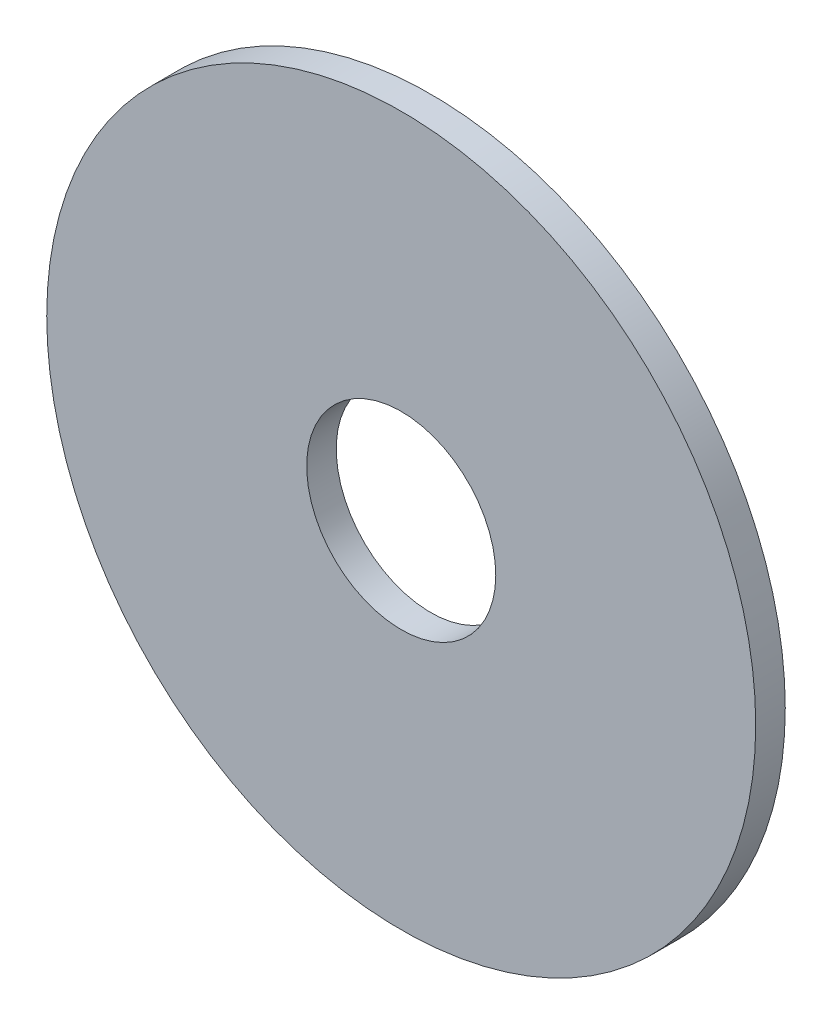
SolidWorks part; units mm, degrees
material "AISI 304"
ref_plane "正面" through (0, 0, 0) normal (0, 0, 1) x (1, 0, 0)
ref_plane "平面" through (0, 0, 0) normal (0, 1, 0) x (1, 0, 0)
ref_plane "右側面" through (0, 0, 0) normal (1, 0, 0) x (0, 0, -1)
sketch "Sketch1" plane through (0, 0, 0) normal (0, 0, 1) x (1, 0, 0)
  circle A0 centre (0, 0) radius 6
extrude "Boss-Extrude1" add sketch "Sketch1" along normal blind 0.5
sketch "Sketch2" plane through (0, 0, 0.5) normal (0, 0, 1) x (1, 0, 0)
  circle A0 centre (0, 0) radius 1.6
extrude "Cut-Extrude1" cut sketch "Sketch2" against normal blind 0.5
